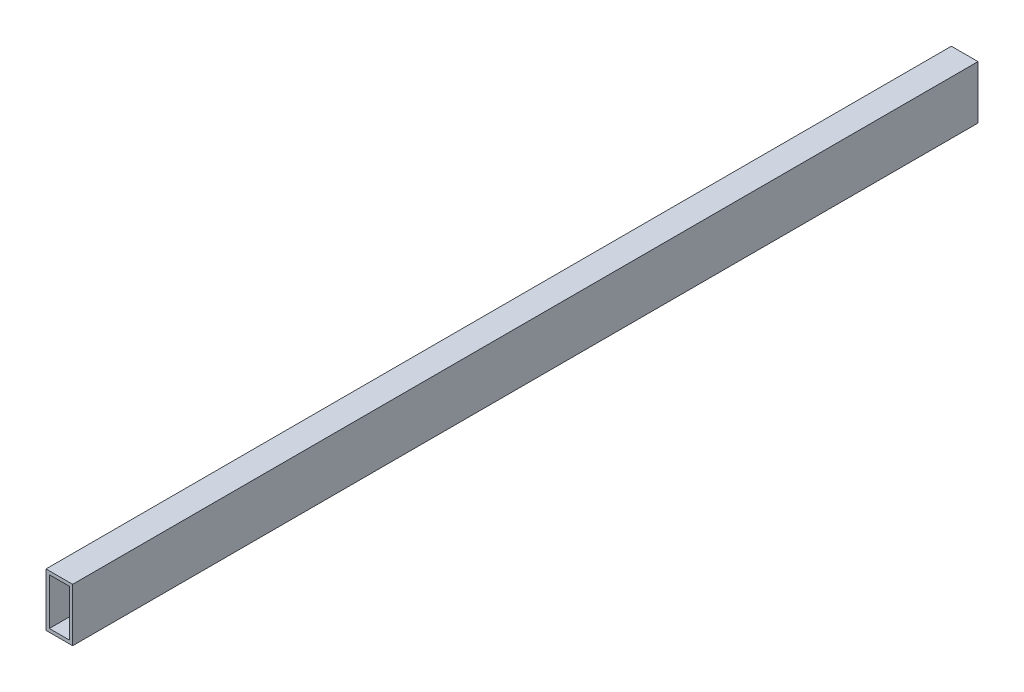
SolidWorks part; units mm, degrees
ref_plane "Front Plane" through (0, 0, 0) normal (0, 0, 1) x (1, 0, 0)
ref_plane "Top Plane" through (0, 0, 0) normal (0, 1, 0) x (1, 0, 0)
ref_plane "Right Plane" through (0, 0, 0) normal (1, 0, 0) x (0, 0, -1)
sketch "Sketch1" plane through (0, 0, 0) normal (0, 0, 1) x (1, 0, 0)
  line L0 (1.5875, 23.8125) -> (11.1125, 23.8125)
  line L1 (0, 0) -> (12.7, 0)
  line L2 (0, 0) -> (0, 25.4)
  line L3 (0, 25.4) -> (12.7, 25.4)
  line L4 (12.7, 0) -> (12.7, 25.4)
  line L5 (11.1125, 1.5875) -> (11.1125, 23.8125)
  line L6 (1.5875, 1.5875) -> (11.1125, 1.5875)
  line L7 (1.5875, 1.5875) -> (1.5875, 23.8125)
  dimension "D1" = 25.4
  dimension "D2" = 1.5875
  dimension "D3" = 12.7
extrude "Boss-Extrude1" add sketch "Sketch1" along normal blind 431.8
